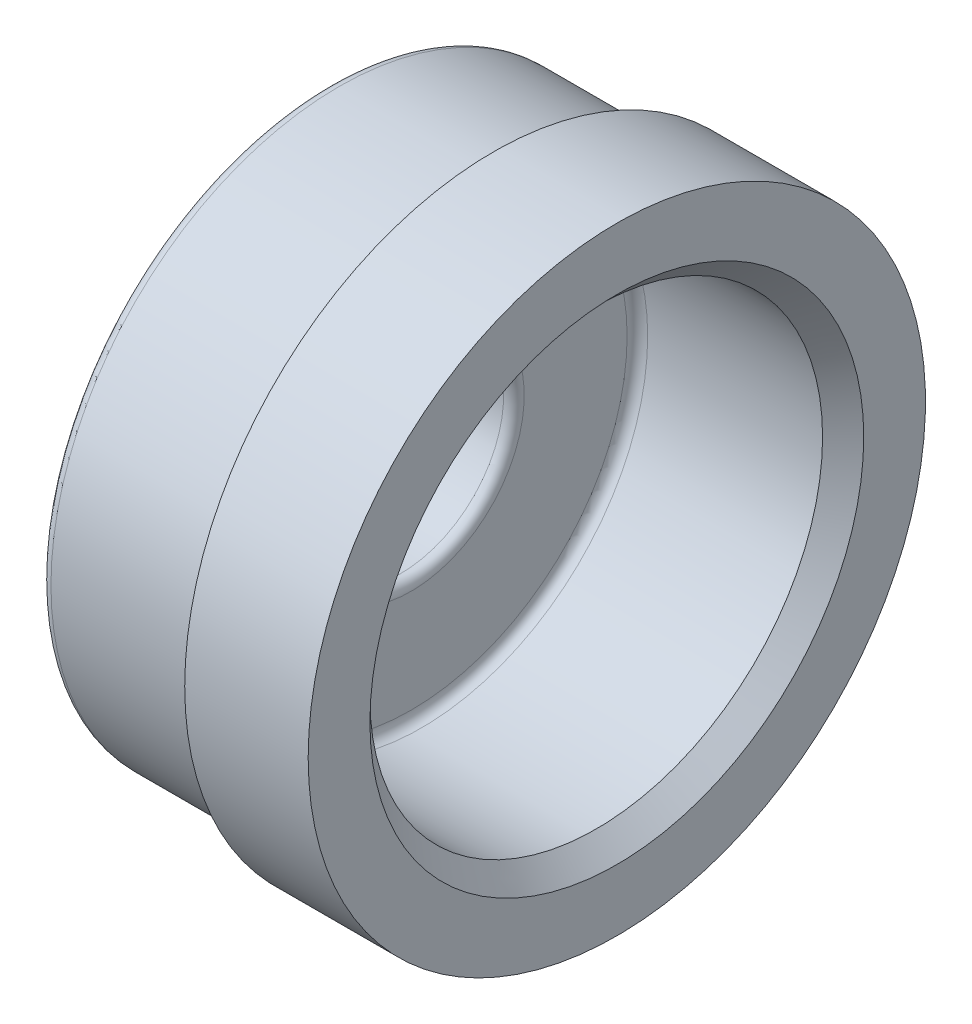
SolidWorks part; units mm, degrees
material "AISI 1020"
ref_plane "Alzado" through (0, 0, 0) normal (0, 0, 1) x (1, 0, 0)
ref_plane "Planta" through (0, 0, 0) normal (0, 1, 0) x (1, 0, 0)
ref_plane "Vista lateral" through (0, 0, 0) normal (1, 0, 0) x (0, 0, -1)
sketch "Croquis1" plane through (0, 0, 0) normal (0, 0, 1) x (1, 0, 0)
  line L0 (0, 0) -> (0, 11) construction
  line L1 (0, 11) -> (10, 11)
  line L2 (10, 11) -> (10, 14)
  line L3 (10, 14) -> (-4, 14) construction
  line L4 (-4, 14) -> (-4, 5)
  line L5 (-4, 5) -> (0, 5)
  line L6 (0, 11) -> (0, 5)
  line L7 (-5.9954, 0) -> (14.9885, 0) construction
  line L8 (-4, 14) -> (4, 14)
  line L9 (4, 14) -> (4, 15)
  line L10 (4, 15) -> (10, 15)
  line L11 (10, 14) -> (10, 15)
  dimension "D1" = 22
  dimension "D2" = 14
  dimension "D3" = 4
  dimension "D4" = 10
  dimension "D5" = 10
  dimension "D6" = 1
  dimension "D7" = 6
revolve "Revolución1" add sketch "Croquis1" angle 360 about L7
fillet "Redondeo1" radius 0.5 4 edges at (-4, 0, 14) (-4, 0, 5) (0, 0, 5) (0, 0, 11)
chamfer "Chaflán1" distance 1 angle 45 1 edges at (10, 0, 11)
